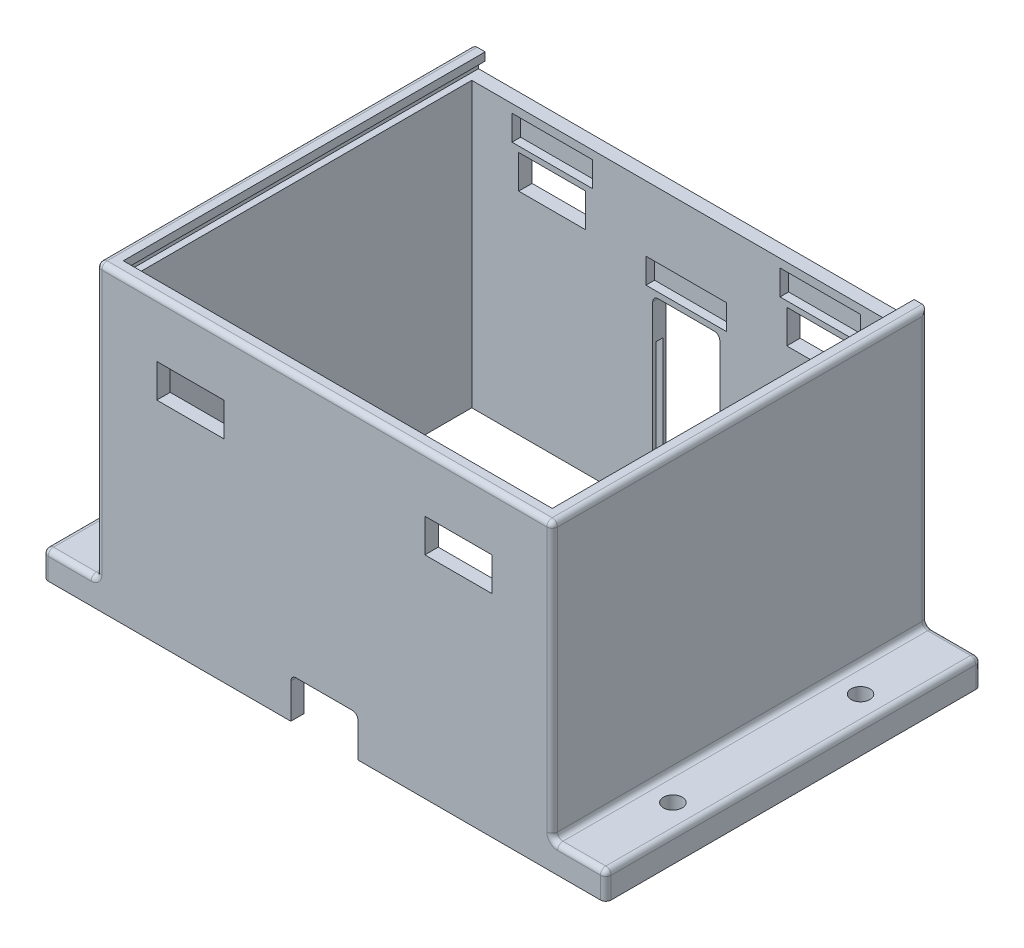
SolidWorks part; units mm, degrees
material "PLA"
ref_plane "Front Plane" through (0, 0, 0) normal (0, 0, 1) x (1, 0, 0)
ref_plane "Top Plane" through (0, 0, 0) normal (0, 1, 0) x (1, 0, 0)
ref_plane "Right Plane" through (0, 0, 0) normal (1, 0, 0) x (0, 0, -1)
sketch "Sketch1" plane through (0, 0, 0) normal (1, 0, 0) x (0, 0, -1)
  line L0 (77, 0) -> (-77, 0) construction
  line L5 (90, 112.5) -> (90, 0)
  line L14 (85, 107.5) -> (85, 0)
  line L17 (-50, 0) -> (-45, 0)
  line L18 (-45, 107.5) -> (-45, 0)
  line L20 (85, 107.5) -> (85, 0)
  line L21 (85, 0) -> (90, 0)
  line L23 (-50, 112.5) -> (90, 112.5)
  line L27 (-50, 112.5) -> (-50, 0)
  line L28 (-50, 112.5) -> (90, 112.5)
  line L29 (-45, 107.5) -> (85, 107.5)
  dimension "D1" = 5
  dimension "D3" = 112.5
  dimension "D5" = 5
extrude "Boss-Extrude1" add sketch "Sketch1" along normal blind 170
ref_plane "Plane1" through (0, 0, -90) normal (0, 0, 1) x (1, 0, 0)
ref_plane "Plane2" through (0, 0, 45) normal (0, 0, -1) x (-1, 0, 0)
sketch "Sketch7" plane through (0, 0, 45) normal (0, 0, -1) x (-1, 0, 0)
  line L0 (-85, 0) -> (-85, 112.5) construction
  line L5 (-170, 0) -> (0, 0) construction
  line L6 (-170, 112.5) -> (0, 112.5) construction
  line L7 (-165, 0) -> (-170, 0)
  line L8 (-170, 0) -> (-170, 112.5)
  line L9 (-165, 0) -> (-165, 112.5)
  line L10 (-165, 112.5) -> (-170, 112.5)
  line L11 (-5, 112.5) -> (0, 112.5)
  line L12 (-5, 0) -> (-5, 112.5)
  line L13 (0, 0) -> (0, 112.5)
  line L14 (-5, 0) -> (0, 0)
  dimension "D1" = 5
  dimension "D2" = 112.5
  dimension "D3" = 80
extrude "Boss-Extrude2" add sketch "Sketch7" along normal blind 130
ref_plane "Plane3" through (0, 122.5, 0) normal (0, 1, 0) x (1, 0, 0)
sketch "Sketch9" plane through (0, 122.5, 0) normal (0, 1, 0) x (1, 0, 0)
  line L0 (170, -50) -> (0, -50) construction
  line L1 (170, -50) -> (170, 90) construction
  line L4 (165, -45) -> (5, -45)
  line L5 (165, -45) -> (165, 85)
  line L6 (165, 85) -> (5, 85)
  line L7 (5, -45) -> (5, 85)
  line L8 (165, -45) -> (5, 85) construction
  line L9 (165, 85) -> (5, -45) construction
  point P6 (85, 20)
  dimension "D1" = 160
  dimension "D2" = 130
  dimension "D3" = 70
  dimension "D4" = 85
extrude "Cut-Extrude2" cut sketch "Sketch9" against normal blind 60
sketch "Sketch10" plane through (80, 0, -90) normal (0, 0, 1) x (1, 0, 0)
  line L1 (-77.5, 109.5) -> (87.5, 109.5)
  line L2 (-77.5, 109.5) -> (-77.5, 105.8)
  line L3 (-77.5, 105.8) -> (87.5, 105.8)
  line L4 (87.5, 109.5) -> (87.5, 105.8)
  line L10 (-80, 112.5) -> (-80, 0) construction
  line L11 (90, 112.5) -> (-80, 112.5) construction
  point P6 (5, 105.8)
  dimension "D1" = 3.7
  dimension "D2" = 3
  dimension "D3" = 165
  dimension "D4" = 85
extrude "Cut-Extrude3" cut sketch "Sketch10" along normal blind 137.5
ref_plane "Plane4" through (170, 0, 0) normal (1, 0, 0) x (0, 0, -1)
sketch "Sketch13" plane through (80, 0, -90) normal (0, 0, 1) x (1, 0, 0)
  line L6 (87.5, 109.5) -> (-77.5, 109.5) construction
  line L7 (-75, 112.5) -> (85, 112.5)
  line L8 (-75, 112.5) -> (-75, 106.5)
  line L9 (-75, 106.5) -> (85, 106.5)
  line L10 (85, 112.5) -> (85, 106.5)
  line L11 (-75, 112.5) -> (85, 106.5) construction
  line L12 (-75, 106.5) -> (85, 112.5) construction
  line L13 (90, 112.5) -> (90, 0) construction
  point P4 (5, 109.5)
  dimension "D1" = 85
  dimension "D2" = 160
  dimension "D3" = 6
extrude "Cut-Extrude4" cut sketch "Sketch13" along normal blind 5
ref_plane "Plane5" through (0, 0, -20) normal (0, 0, 1) x (1, 0, 0)
sketch "Sketch15" plane through (0, 0, -20) normal (0, 0, 1) x (1, 0, 0)
  line L0 (85, 0) -> (85, 112.5) construction
  line L1 (0, 0) -> (-20, 0)
  line L2 (0, 0) -> (0, 10)
  line L3 (0, 10) -> (-20, 10)
  line L4 (-20, 0) -> (-20, 10)
  line L5 (170, 0) -> (0, 0) construction
  line L6 (170, 112.5) -> (0, 112.5) construction
  line L7 (190, 0) -> (190, 10)
  line L8 (170, 10) -> (190, 10)
  line L9 (170, 0) -> (170, 10)
  line L10 (170, 0) -> (190, 0)
  dimension "D1" = 10
  dimension "D2" = 20
extrude "Boss-Extrude3" add sketch "Sketch15" along normal mid plane 140
sketch "Sketch16" plane through (0, 0, 50) normal (0, 0, 1) x (1, 0, 0)
  line L0 (0, 112.5) -> (0, 10) construction
  line L1 (22.5, 78.75) -> (47.5, 78.75)
  line L2 (22.5, 78.75) -> (22.5, 91.25)
  line L3 (22.5, 91.25) -> (47.5, 91.25)
  line L4 (47.5, 78.75) -> (47.5, 91.25)
  line L5 (22.5, 78.75) -> (47.5, 91.25) construction
  line L6 (22.5, 91.25) -> (47.5, 78.75) construction
  line L7 (85, 112.5) -> (85, 0) construction
  line L8 (170, 112.5) -> (0, 112.5) construction
  line L9 (190, 0) -> (-20, 0) construction
  line L10 (147.5, 91.25) -> (122.5, 78.75) construction
  line L11 (147.5, 78.75) -> (122.5, 91.25) construction
  line L12 (122.5, 78.75) -> (122.5, 91.25)
  line L13 (147.5, 91.25) -> (122.5, 91.25)
  line L14 (147.5, 78.75) -> (147.5, 91.25)
  line L15 (147.5, 78.75) -> (122.5, 78.75)
  point P0 (35, 85)
  point P17 (135, 85)
  dimension "D1" = 35
  dimension "D2" = 12.5
  dimension "D3" = 85
  dimension "D4" = 25
extrude "Cut-Extrude5" cut sketch "Sketch16" against normal blind 5
hole_wizard "M6 Clearance Hole1" positions "Sketch20" profile "Sketch21" hole size "M6" standard "ANSI Metric" end condition up to next
sketch "Sketch20" plane through (0, 10, 0) normal (0, 1, 0) x (1, 0, 0)
  line L0 (190, -50) -> (190, 90) construction
  point P0 (-10, -15)
  point P2 (-10, 55)
  point P4 (180, 55)
  point P6 (180, -15)
  dimension "D1" = 10
  dimension "D2" = 10
  dimension "D3" = 35
  dimension "D4" = 105
sketch "Sketch21" plane through (-10, 10, 15) normal (1, 0, 0) x (0, 0, 1)
  line L0 (0, 0) -> (0, 10)
  line L1 (0, 10) -> (3.5, 10)
  line L2 (3.5, 10) -> (3.5, 0)
  line L5 (3.5, 0) -> (0, 0)
  line L11 (0, -6.35) -> (0, 107.95) construction
  dimension "Thru Hole Dia." = 7
  dimension "Thru Hole Depth" = 10
ref_plane "Plane6" through (35, 0, 0) normal (1, 0, 0) x (0, 0, -1)
ref_plane "Center Plane" through (85, 0, 0) normal (1, 0, 0) x (0, 0, -1)
mirror "Mirror2" about plane through (0, 0, -20) normal (0, 0, 1) of "Cut-Extrude5"
sketch "Sketch26" plane through (0, 0, -20) normal (0, 0, 1) x (1, 0, 0)
  line L1 (150, 93.325) -> (120, 93.325)
  line L2 (150, 93.325) -> (150, 102.675)
  line L3 (150, 102.675) -> (120, 102.675)
  line L4 (120, 93.325) -> (120, 102.675)
  line L5 (150, 93.325) -> (120, 102.675) construction
  line L6 (150, 102.675) -> (120, 93.325) construction
  line L7 (50, 102.675) -> (20, 102.675)
  line L8 (50, 102.675) -> (50, 93.325)
  line L9 (50, 93.325) -> (20, 93.325)
  line L10 (20, 102.675) -> (20, 93.325)
  line L11 (50, 102.675) -> (20, 93.325) construction
  line L12 (50, 93.325) -> (20, 102.675) construction
  line L16 (35, -61.875) -> (35, 61.875) construction
  line L17 (190, 0) -> (-20, 0) construction
  point P0 (135, 98)
  point P5 (35, 98)
  dimension "D1" = 100
  dimension "D2" = 30
  dimension "D3" = 9.35
  dimension "D4" = 98
extrude "Cut-Extrude6" cut sketch "Sketch26" against normal mid plane 136.4
sketch "Sketch27" plane through (0, 0, -20) normal (0, 0, 1) x (1, 0, 0)
  line L0 (190, 0) -> (-20, 0) construction
  line L1 (-20, 10) -> (-20, 0) construction
  line L2 (70, 17.125) -> (100, 17.125)
  line L3 (70, 17.125) -> (70, 26.475)
  line L4 (70, 26.475) -> (100, 26.475)
  line L5 (100, 17.125) -> (100, 26.475)
  line L6 (70, 17.125) -> (100, 26.475) construction
  line L7 (70, 26.475) -> (100, 17.125) construction
  point P4 (85, 21.8)
  dimension "D1" = 30
  dimension "D2" = 9.35
  dimension "D3" = 105
  dimension "D4" = 21.8
extrude "Cut-Extrude8" cut sketch "Sketch27" along normal blind 68.2
ref_plane "Plane8" through (0, 0, 50) normal (0, 0, -1) x (-1, 0, 0)
sketch "Sketch28" plane through (0, 0, 50) normal (0, 0, -1) x (-1, 0, 0)
  line L0 (-72.5, 0) -> (-72.5, 13)
  line L1 (-190, 0) -> (20, 0) construction
  line L2 (-74.5, 15) -> (-95.5, 15)
  line L3 (-97.5, 13) -> (-97.5, 0)
  line L4 (-72.5, 0) -> (-97.5, 0)
  arc A0 (-95.5, 15) -> (-97.5, 13) centre (-95.5, 13) ccw
  arc A1 (-72.5, 13) -> (-74.5, 15) centre (-74.5, 13) ccw
  point P4 (-85, 0)
  point P9 (-97.5, 15)
  point P12 (-72.5, 15)
  dimension "D4" = 2
  dimension "D1" = 15
  dimension "D2" = 25
  dimension "D3" = 12.5
extrude "Cut-Extrude10" cut sketch "Sketch28" along normal blind 5
sketch "Sketch29" plane through (0, 0, -90) normal (0, 0, 1) x (1, 0, 0)
  line L0 (190, 0) -> (-20, 0) construction
  line L3 (190, 0) -> (190, 10) construction
  line L4 (95.5, 52.5) -> (74.5, 52.5)
  line L5 (97.5, 54.5) -> (97.5, 68)
  line L6 (95.5, 70) -> (74.5, 70)
  line L7 (72.5, 54.5) -> (72.5, 68)
  line L8 (97.5, 52.5) -> (72.5, 70) construction
  line L9 (97.5, 70) -> (72.5, 52.5) construction
  arc A0 (72.5, 54.5) -> (74.5, 52.5) centre (74.5, 54.5) ccw
  arc A1 (74.5, 70) -> (72.5, 68) centre (74.5, 68) ccw
  arc A2 (97.5, 54.5) -> (95.5, 52.5) centre (95.5, 54.5) cw
  arc A3 (97.5, 68) -> (95.5, 70) centre (95.5, 68) ccw
  point P2 (85, 0)
  point P6 (85, 61.25)
  dimension "D3" = 2
  dimension "D1" = 25
  dimension "D2" = 17.5
  dimension "D4" = 61.25
  dimension "D5" = 105
extrude "Cut-Extrude11" cut sketch "Sketch29" along normal blind 5
sketch "Sketch30" plane through (0, 0, -20) normal (0, 0, 1) x (1, 0, 0)
  line L0 (190, 0) -> (190, 10) construction
  line L1 (100, 81.475) -> (70, 81.475)
  line L2 (100, 81.475) -> (100, 72.125)
  line L3 (100, 72.125) -> (70, 72.125)
  line L4 (70, 81.475) -> (70, 72.125)
  line L5 (100, 81.475) -> (70, 72.125) construction
  line L6 (100, 72.125) -> (70, 81.475) construction
  line L7 (190, 0) -> (-20, 0) construction
  point P0 (85, 76.8)
  point P9 (85, 0)
  dimension "D1" = 9.35
  dimension "D2" = 30
  dimension "D3" = 105
  dimension "D4" = 76.8
extrude "Cut-Extrude12" cut sketch "Sketch30" against normal blind 68.2
sketch "Sketch31" plane through (0, 0, 0) normal (0, 1, 0) x (1, 0, 0)
  line L0 (165, 85) -> (5, 85) construction
  line L3 (97.5, 86.25) -> (100.5, 86.25)
  line L4 (97.5, 85) -> (72.5, 85)
  line L5 (97.5, 85) -> (97.5, 86.25)
  line L6 (97.5, 90) -> (72.5, 90)
  line L7 (72.5, 85) -> (72.5, 86.25)
  line L8 (97.5, 85) -> (72.5, 90) construction
  line L9 (97.5, 90) -> (72.5, 85) construction
  line L11 (97.5, 88.75) -> (100.5, 88.75)
  line L12 (100.5, 86.25) -> (100.5, 88.75)
  line L13 (97.5, 88.75) -> (97.5, 90)
  line L14 (85, 85) -> (85, 90) construction
  line L18 (72.5, 88.75) -> (72.5, 90)
  line L19 (190, -50) -> (190, 90) construction
  line L20 (72.5, 86.25) -> (69.5, 86.25)
  line L21 (69.5, 86.25) -> (69.5, 88.75)
  line L22 (72.5, 88.75) -> (69.5, 88.75)
  point P6 (85, 87.5)
  point P12 (85, 85)
  dimension "D1" = 25
  dimension "D2" = 5
  dimension "D3" = 2.5
  dimension "D4" = 2.5
  dimension "D5" = 3
  dimension "D6" = 105
  dimension "D9" = 1.25
extrude "Cut-Extrude14" cut sketch "Sketch31" along normal blind 54.5
fillet "Fillet1" radius 2 19 edges at (180, 10, -90) (180, 10, 50) (-10, 10, -90) (-10, 10, 50) (170, 112.5, -20) (85, 112.5, 50) (0, 112.5, -20) (190, 10, -20) (170, 10, -20) (-20, 10, -20) (0, 10, -20) (0, 61.25, 50) (170, 61.25, 50) (0, 61.25, -90) (170, 61.25, -90) (190, 5, -90) (190, 5, 50) (-20, 5, -90) (-20, 5, 50)
